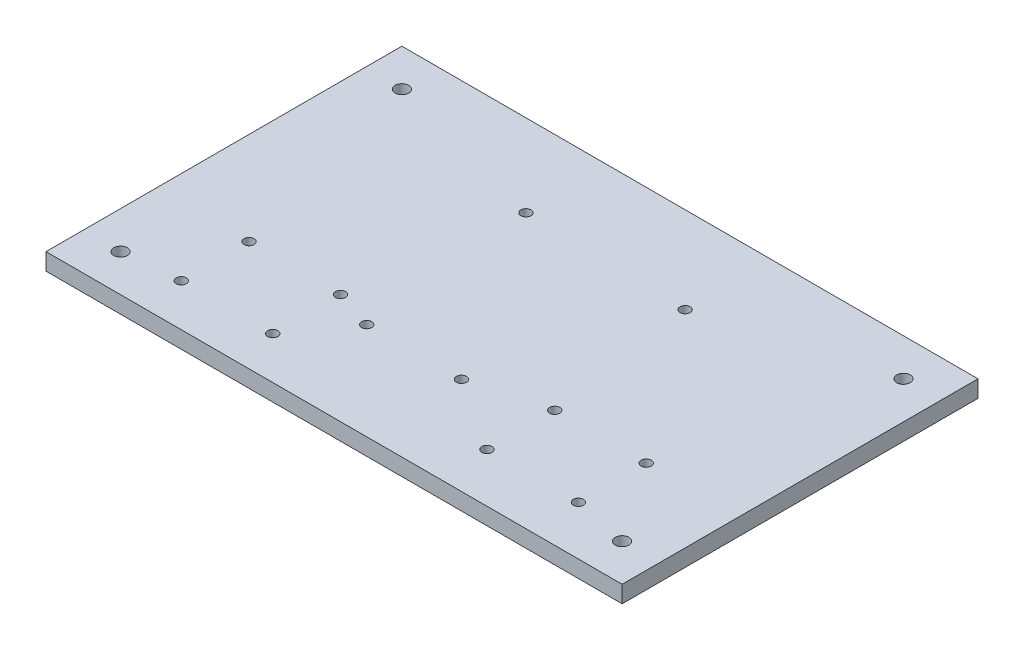
SolidWorks part; units mm, degrees
ref_plane "正面" through (0, 0, 0) normal (0, 0, 1) x (1, 0, 0)
ref_plane "平面" through (0, 0, 0) normal (0, 1, 0) x (1, 0, 0)
ref_plane "右側面" through (0, 0, 0) normal (1, 0, 0) x (0, 0, -1)
sketch "ｽｹｯﾁ1" plane through (0, 0, 0) normal (0, 1, 0) x (1, 0, 0)
  line L0 (85, 100) -> (85, 43.8318) construction
  line L1 (0, 0) -> (170, 0)
  line L2 (0, 0) -> (0, 105)
  line L3 (0, 105) -> (170, 105)
  line L4 (170, 0) -> (170, 105)
  line L5 (5, 100) -> (165, 100) construction
  line L6 (5, 100) -> (5, 5) construction
  line L7 (5, 5) -> (165, 5) construction
  line L8 (165, 100) -> (165, 5) construction
  line L9 (5, 52.5) -> (92.5057, 52.5) construction
  line L10 (25, 100) -> (5, 80) construction
  line L11 (58.33, 94.7) -> (111.67, 94.7)
  line L12 (58.33, 94.7) -> (58.33, 26.11)
  line L13 (58.33, 26.11) -> (111.67, 26.11)
  line L14 (111.67, 94.7) -> (111.67, 26.11)
  line L15 (57, 9) -> (23, 9)
  line L16 (57, 9) -> (57, 36)
  line L17 (57, 36) -> (23, 36)
  line L18 (23, 9) -> (23, 36)
  line L19 (25, 5) -> (5, 25) construction
  line L20 (23, 22.5) -> (20, 22.5) construction
  line L21 (113, 11) -> (147, 11)
  line L22 (113, 11) -> (113, 38)
  line L23 (113, 38) -> (147, 38)
  line L24 (147, 11) -> (147, 38)
  line L25 (147, 24.5) -> (141.8572, 24.5) construction
  circle A0 centre (85, 51.5) radius 11
  circle A1 centre (70, 75.5) radius 11
  circle A2 centre (20, 75.5) radius 11
  circle A3 centre (40, 58) radius 11
  circle A4 centre (11, 94) radius 2
  circle A6 centre (11, 11) radius 2
  circle A9 centre (159, 11) radius 2
  circle A12 centre (159, 94) radius 2
  circle A18 centre (100, 75.5) radius 7.85
  circle A19 centre (130, 58) radius 7.85
  circle A20 centre (150, 75.5) radius 7.85
  circle A21 centre (54.4, 12.5) radius 1.5
  circle A22 centre (27.4, 12.5) radius 1.5
  circle A23 centre (54.4, 32.5) radius 1.5
  circle A24 centre (27.4, 32.5) radius 1.5
  circle A25 centre (60.88, 80.73) radius 1.5
  circle A26 centre (65.97, 28.66) radius 1.5
  circle A27 centre (93.92, 28.66) radius 1.5
  circle A28 centre (109.12, 79.45) radius 1.5
  circle A29 centre (115.6, 34.5) radius 1.5
  circle A31 centre (142.6, 34.5) radius 1.5
  circle A32 centre (142.6, 14.5) radius 1.5
  circle A33 centre (115.6, 14.5) radius 1.5
  point P17 (85, 94.7)
  dimension "D10" = 2.6
  dimension "D11" = 23
  dimension "D15" = 3
  dimension "D16" = 22
  dimension "D17" = 15
  dimension "D24" = 4
  dimension "D30" = 27
  dimension "D19" = 3
  dimension "D35" = 13.97
  dimension "D36" = 3
  dimension "D37" = 2.55
  dimension "D38" = 3
  dimension "D39" = 3
  dimension "D43" = 3
  dimension "D46" = 3
  dimension "D47" = 3
  dimension "D1" = 170
  dimension "D2" = 105
  dimension "D3" = 5
  dimension "D4" = 5
  dimension "D5" = 5
  dimension "D6" = 5
  dimension "D7" = 53.34
  dimension "D8" = 10.3
  dimension "D9" = 68.59
  dimension "D12" = 27
  dimension "D13" = 9
  dimension "D14" = 34
  dimension "D18" = 1
  dimension "D20" = 11
  dimension "D21" = 11
  dimension "D22" = 22
  dimension "D23" = 11
  dimension "D25" = 35
  dimension "D26" = 15
  dimension "D27" = 28
  dimension "D28" = 20
  dimension "D29" = 20
  dimension "D31" = 34
  dimension "D32" = 28
  dimension "D33" = 4.4
  dimension "D34" = 3.5
  dimension "D40" = 2.55
  dimension "D41" = 7.64
  dimension "D42" = 35.59
  dimension "D44" = 2.55
  dimension "D45" = 15.25
  dimension "D48" = 2.6
  dimension "D49" = 4.4
  dimension "D50" = 3.5
extrude "ﾎﾞｽ - 押し出し1" add sketch "ｽｹｯﾁ1" along normal blind 5
